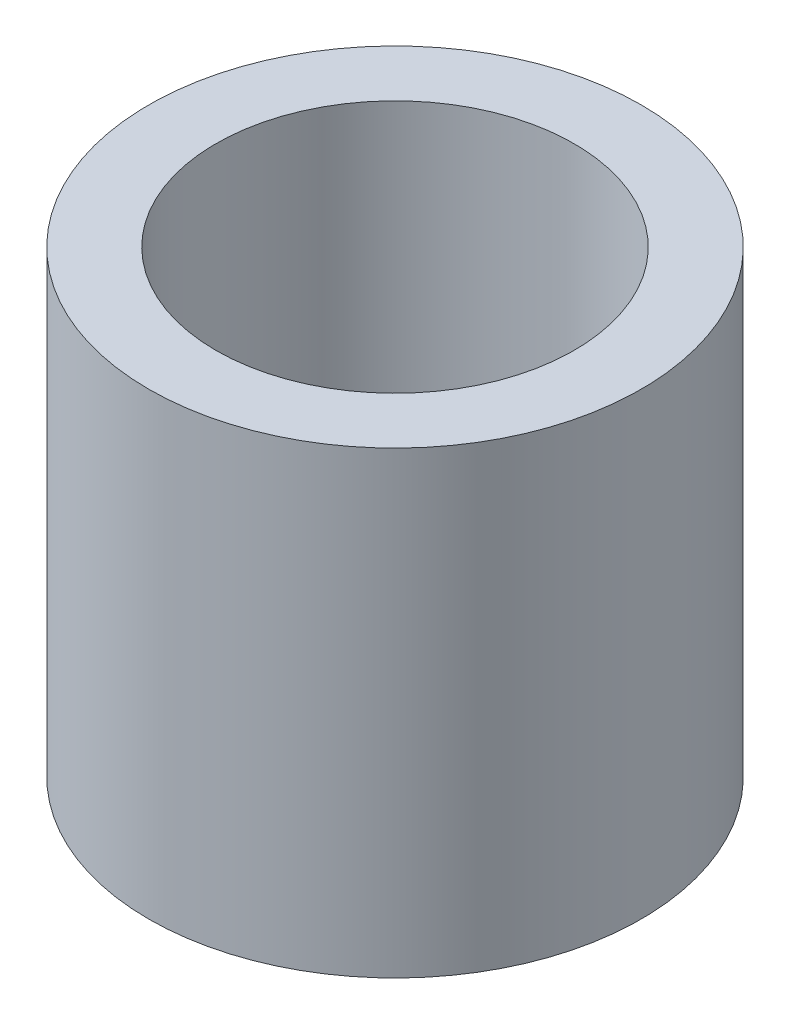
SolidWorks part; units mm, degrees
material "Cast Alloy Steel"
ref_plane "Front Plane" through (0, 0, 0) normal (0, 0, 1) x (1, 0, 0)
ref_plane "Top Plane" through (0, 0, 0) normal (0, 1, 0) x (1, 0, 0)
ref_plane "Right Plane" through (0, 0, 0) normal (1, 0, 0) x (0, 0, -1)
sketch "Sketch1" plane through (0, 0, 0) normal (0, 1, 0) x (1, 0, 0)
  circle A0 centre (0, 0) radius 4
  circle A1 centre (0, 0) radius 5.5
  dimension "D1" = 8
  dimension "D2" = 1.5
extrude "Boss-Extrude1" add sketch "Sketch1" along normal mid plane 10.25
